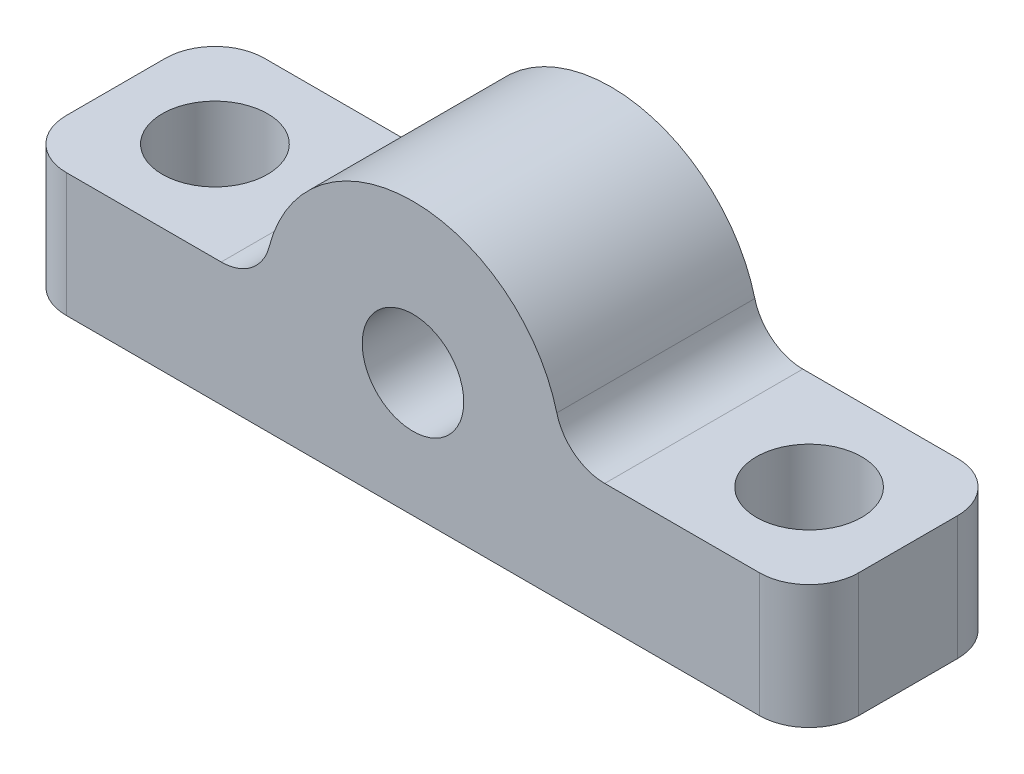
SolidWorks part; units mm, degrees
material "PE Low Density Film"
ref_plane "Front Plane" through (0, 0, 0) normal (0, 0, 1) x (1, 0, 0)
ref_plane "Top Plane" through (0, 0, 0) normal (0, 1, 0) x (1, 0, 0)
ref_plane "Right Plane" through (0, 0, 0) normal (1, 0, 0) x (0, 0, -1)
sketch "Sketch2" plane through (0, 0, 0) normal (0, 0, 1) x (1, 0, 0)
  line L0 (6, 2.5) -> (16, 2.5)
  line L1 (-16, -2.5) -> (16, -2.5)
  line L2 (-16, -2.5) -> (-16, 2.5)
  line L3 (-16, 2.5) -> (-6, 2.5)
  line L4 (16, -2.5) -> (16, 2.5)
  line L5 (-16, -2.5) -> (16, 2.5) construction
  line L6 (-16, 2.5) -> (16, -2.5) construction
  line L7 (-6, 2.5) -> (0, 2.5) construction
  arc A0 (-6, 2.5) -> (6, 2.5) centre (0, 2.5) cw
  circle A1 centre (0, 2.5) radius 2.05
  point P0 (0, 0)
  dimension "D1" = 4.1
  dimension "D3" = 6
  dimension "D2" = 5
  dimension "D4" = 10
extrude "Boss-Extrude1" add sketch "Sketch2" along normal blind 8
sketch "Sketch3" plane through (0, 2.5, 0) normal (0, 1, 0) x (1, 0, 0)
  line L0 (-6, 0) -> (-16, 0) construction
  line L1 (-16, -8) -> (-16, 0) construction
  line L2 (16, -8) -> (16, 0) construction
  circle A0 centre (12, -4) radius 2.125
  circle A1 centre (-12, -4) radius 2.125
  dimension "D1" = 4
  dimension "D2" = 4
  dimension "D3" = 4
  dimension "D4" = 4.25
extrude "Cut-Extrude1" cut sketch "Sketch3" against normal blind 8
fillet "Fillet1" radius 2 6 edges at (16, 0, 0) (16, 0, 8) (6, 2.5, 4) (-6, 2.5, 4) (-16, 0, 0) (-16, 0, 8)
